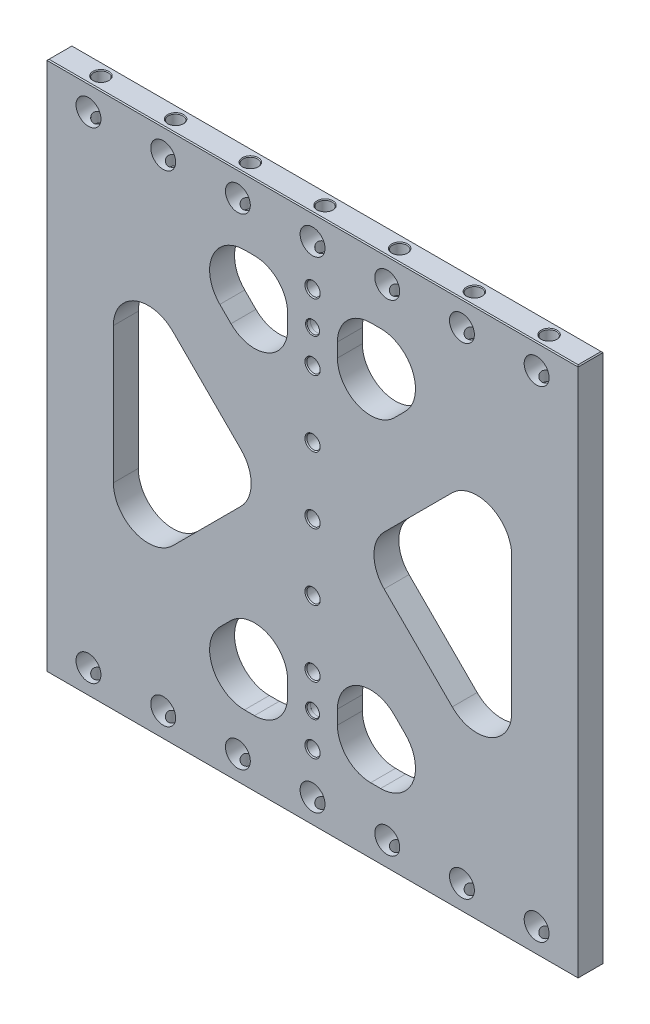
SolidWorks part; units mm, degrees
material "6061-T6 Al"
ref_plane "Front Plane" through (0, 0, 0) normal (0, 0, 1) x (1, 0, 0)
ref_plane "Top Plane" through (0, 0, 0) normal (0, 1, 0) x (1, 0, 0)
ref_plane "Right Plane" through (0, 0, 0) normal (1, 0, 0) x (0, 0, -1)
sketch "Sketch2" plane through (0, 0, 0) normal (0, 0, 1) x (1, 0, 0)
  line L0 (-203.2, -203.2) -> (203.2, 203.2) construction
  line L1 (-203.2, 203.2) -> (203.2, 203.2)
  line L2 (-203.2, 203.2) -> (-203.2, -203.2)
  line L3 (-203.2, -203.2) -> (203.2, -203.2)
  line L4 (203.2, 203.2) -> (203.2, -203.2)
  point P4 (0, 0)
  dimension "D1" = 406.4
  dimension "D2" = 406.4
extrude "Extrude1" add sketch "Sketch2" along normal mid plane 19.05
sketch "Sketch8" plane through (0, 0, 9.525) normal (0, 0, 1) x (1, 0, 0)
  line L0 (-203.2, 203.2) -> (203.2, -203.2) construction
  line L1 (203.2, 203.2) -> (-203.2, -203.2) construction
  line L2 (-152.4, 116.479) -> (-35.921, 0)
  line L3 (-35.921, 0) -> (-152.4, -116.479)
  line L4 (-152.4, -116.479) -> (-152.4, 116.479)
  line L5 (-116.479, 152.4) -> (0, 35.921)
  line L6 (0, 35.921) -> (116.479, 152.4)
  line L7 (116.479, 152.4) -> (-116.479, 152.4)
  line L8 (152.4, 116.479) -> (152.4, -116.479)
  line L9 (152.4, -116.479) -> (35.921, 0)
  line L10 (35.921, 0) -> (152.4, 116.479)
  line L11 (0, -35.921) -> (-116.479, -152.4)
  line L12 (-116.479, -152.4) -> (116.479, -152.4)
  line L13 (116.479, -152.4) -> (0, -35.921)
  line L14 (0, -35.921) -> (-35.921, 0) construction
  line L15 (-35.921, 0) -> (0, 35.921) construction
  line L16 (0, 35.921) -> (0, 0) construction
  line L17 (0, 0) -> (0, -35.921) construction
  line L18 (35.921, 0) -> (0, 0) construction
  line L19 (0, 0) -> (-35.921, 0) construction
  line L20 (-203.2, 203.2) -> (-203.2, -203.2) construction
  line L21 (203.2, 203.2) -> (-203.2, 203.2) construction
  point P19 (-17.9605, 17.9605)
  point P23 (-17.9605, -17.9605)
  point P24 (-203.2, 0)
  dimension "D1" = 50.8
  dimension "D2" = 50.8
  dimension "D3" = 50.8
extrude "Triangles -- Cut-Extrude2" cut sketch "Sketch8" against normal through all
fillet "Triangles -- Fillet1" radius 26.67 10 edges at (-152.4, -116.479, 0) (-35.921, 0, 0) (-116.479, -152.4, 0) (116.479, -152.4, 0) (35.921, 0, 0) (152.4, -116.479, 0) (152.4, 116.479, 0) (116.479, 152.4, 0) (-116.479, 152.4, 0) (-152.4, 116.479, 0)
sketch "Sketch14" plane through (0, 0, 9.525) normal (0, 0, 1) x (1, 0, 0)
  line L0 (203.2, 203.2) -> (-203.2, 203.2) construction
  line L1 (-19.05, 203.2) -> (19.05, 203.2)
  line L2 (-19.05, 203.2) -> (-19.05, -203.2)
  line L3 (-19.05, -203.2) -> (19.05, -203.2)
  line L4 (19.05, 203.2) -> (19.05, -203.2)
  line L5 (-203.2, -203.2) -> (203.2, -203.2) construction
  line L6 (-19.05, 0) -> (19.05, 0) construction
  point P10 (0, 0)
  dimension "D1" = 38.1
extrude "Extrude5" add sketch "Sketch14" against normal through all
fillet "Fillet3" radius 25.4 8 edges at (19.05, -152.4, 0) (-19.05, -152.4, 0) (19.05, 152.4, 0) (-19.05, 152.4, 0) (-19.05, -54.971, 0) (19.05, -54.971, 0) (19.05, 54.971, 0) (-19.05, 54.971, 0)
hole_wizard "CBORE for 3/8 Socket Head Cap Screw1" positions "Sketch16" profile "Sketch15" counterbore size "3/8" standard "Ansi Inch" end condition through all
sketch "Sketch16" plane through (39.3165, 12.506, -9.525) normal (0, 0, 1) x (1, 0, 0)
  point P1 (-39.3165, -12.506)
sketch "Sketch15" plane through (0, 0, -9.525) normal (1, 0, 0) x (0, 1, 0)
  line L0 (0, 0) -> (0, 19.05)
  line L1 (5.1587, 18.264) -> (5.842, 19.05)
  line L2 (5.1587, 18.264) -> (5.1587, 4.318)
  line L3 (5.1587, 4.318) -> (8.7312, 4.318)
  line L4 (8.7312, 4.318) -> (8.7312, 0)
  line L5 (8.7312, 0) -> (0, 0)
  line L11 (0, -6.35) -> (0, 107.95) construction
  line L12 (5.842, 19.05) -> (0, 19.05)
  line L13 (-5.1587, 18.264) -> (-5.842, 19.05) construction
  dimension "Thru Hole Dia." = 10.3175
  dimension "Thru Hole Depth" = 19.05
  dimension "C'Bore Dia." = 17.4625
  dimension "C'Bore Depth" = 4.318
  dimension "Far C'Sink Dia." = 11.684
  dimension "Far C'Sink Angle" = 82
pattern_linear "LPattern5" count 4 spacing 50.8 along (0, 1, 0) count 4 spacing 50.8 along (0, -1, 0) of "CBORE for 3/8 Socket Head Cap Screw1"
hole_wizard "3/4 (0.75) Diameter Hole1" positions "Sketch11" profile "Sketch10" hole size "3/4" standard "Ansi Inch" end condition through all
sketch "Sketch11" plane through (0, 0, 9.525) normal (0, 0, 1) x (1, 0, 0)
  line L0 (0, 0) -> (0, -184.15) construction
  line L2 (-203.2, -203.2) -> (203.2, -203.2) construction
  point P0 (0, -184.15)
  dimension "D1" = 19.05
sketch "Sketch10" plane through (0, -184.15, 9.525) normal (1, 0, 0) x (0, -1, 0)
  line L0 (0, 0) -> (0, 19.05)
  line L1 (0, 19.05) -> (9.525, 19.05)
  line L2 (9.525, 19.05) -> (9.525, 0)
  line L5 (9.525, 0) -> (0, 0)
  line L11 (0, -6.35) -> (0, 107.95) construction
  dimension "Thru Hole Dia." = 19.05
  dimension "Thru Hole Depth" = 19.05
hole_wizard "7/16 (0.4375) Diameter Hole1" positions "Sketch13" profile "Sketch12" hole size "7/16" standard "Ansi Inch"
sketch "Sketch13" plane through (0, -203.2, 0) normal (0, -1, 0) x (1, 0, 0)
  point P0 (0, 0)
sketch "Sketch12" plane through (0, -203.2, 0) normal (1, 0, 0) x (0, 0, -1)
  line L0 (0, 0) -> (0, 38.2635)
  line L1 (0, 38.2635) -> (5.5562, 34.925)
  line L2 (5.5562, 34.925) -> (5.5562, 0.6209)
  line L3 (5.5562, 0.6209) -> (6.096, 0)
  line L5 (6.096, 0) -> (0, 0)
  line L6 (-5.5562, 0.6209) -> (-6.096, 0) construction
  line L10 (0, 38.2635) -> (-5.5563, 34.925) construction
  line L11 (0, -6.35) -> (0, 107.95) construction
  dimension "Hole Dia." = 11.1125
  dimension "Hole Depth" = 34.925
  dimension "Near C'Sink Dia." = 12.192
  dimension "Near C'Sink Angle" = 82
  dimension "Drill Angle" = 118
pattern_linear "LPattern4" count 4 spacing 57.15 along (1, 0, 0) count 4 spacing 57.15 along (-1, 0, 0) of "7/16 (0.4375) Diameter Hole1", "3/4 (0.75) Diameter Hole1"
mirror "Mirror2" about plane through (0, 0, 0) normal (0, 1, 0) of "3/4 (0.75) Diameter Hole1", "7/16 (0.4375) Diameter Hole1", "LPattern4"
hole_wizard "3/8 (0.375) Pin + Lead-In Hole1" positions "Sketch18" profile "Sketch17" counterbore size "3/8" standard "Ansi Inch" end condition through all
sketch "Sketch18" plane through (0, 0, 9.525) normal (0, 0, 1) x (1, 0, 0)
  line L11 (0, 0) -> (0, 127) construction
  line L14 (0, -127) -> (0, 0) construction
  point P0 (0, 127)
  point P17 (0, -127)
  dimension "D1" = 127
  dimension "D2" = 127
sketch "Sketch17" plane through (0, 127, 9.525) normal (1, 0, 0) x (0, -1, 0)
  line L0 (0, 0) -> (0, 19.05)
  line L1 (0, 19.05) -> (4.7625, 19.05)
  line L3 (4.7625, 19.05) -> (4.7625, 3.175)
  line L4 (4.7879, 3.175) -> (4.7625, 3.175)
  line L5 (4.7879, 3.175) -> (4.7879, 0.6282)
  line L6 (4.7879, 0.6282) -> (5.334, 0)
  line L7 (5.334, 0) -> (0, 0)
  line L8 (-4.7879, 0.6282) -> (-5.334, 0) construction
  line L11 (0, -6.35) -> (0, 107.95) construction
  dimension "Thru Hole Dia." = 9.525
  dimension "Thru Hole Depth" = 19.05
  dimension "C'Bore Dia." = 9.5758
  dimension "C'Bore Depth" = 3.175
  dimension "Near C'Sink Dia." = 10.668
  dimension "Near C'Sink Angle" = 82
chamfer "Chamfer1" distance 0.762 angle 45 8 edges at (-203.2, -203.2, 0) (0, -203.2, 9.525) (0, -203.2, -9.525) (203.2, -203.2, 0) (-203.2, 203.2, 0) (0, 203.2, -9.525) (0, 203.2, 9.525) (203.2, 203.2, 0)
